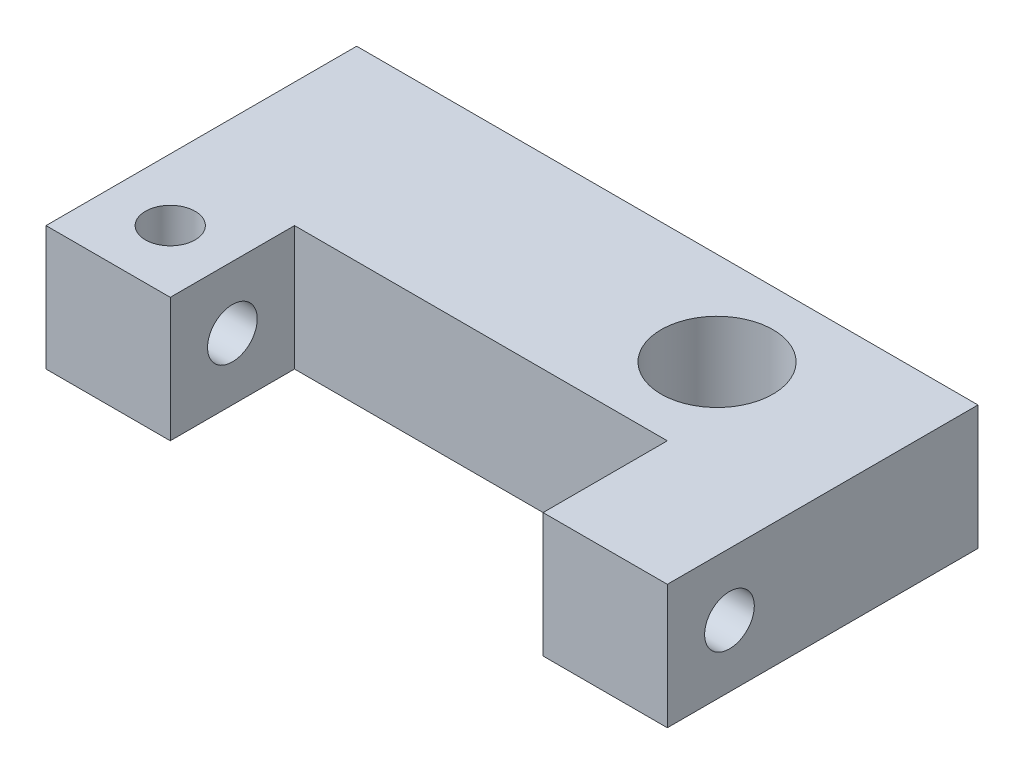
SolidWorks part; units mm, degrees
ref_plane "Plan de face" through (0, 0, 0) normal (0, 0, 1) x (1, 0, 0)
ref_plane "Plan de dessus" through (0, 0, 0) normal (0, 1, 0) x (1, 0, 0)
ref_plane "Plan de droite" through (0, 0, 0) normal (1, 0, 0) x (0, 0, -1)
sketch "Esquisse1" plane through (0, 0, 0) normal (0, 0, 1) x (1, 0, 0)
  line L5 (0, -3.3) -> (0, 3.3) construction
  line L6 (-10, 4) -> (10, 4)
  line L11 (-10, 4) -> (-10, 0)
  line L12 (-10, 0) -> (2.2, 0)
  line L13 (10, 4) -> (10, 0)
  line L14 (-10, 4) -> (10, 0) construction
  line L15 (-10, 0) -> (10, 4) construction
  line L16 (5.5, 0) -> (-5.5, 0) construction
  line L17 (7, 0) -> (10, 0)
  line L19 (2.2, 0) -> (2.2, -2)
  line L20 (2.2, -2) -> (7, -2)
  line L21 (7, 0) -> (7, -2)
  point P0 (0, 0)
  point P1 (0, 2)
  dimension "D1" = 4
  dimension "D2" = 2
  dimension "D3" = 4.8
  dimension "D4" = 20
  dimension "D5" = 3
extrude "Boss.-Extru.1" add sketch "Esquisse1" against normal blind 6
sketch "Esquisse2" plane through (0, 0, 0) normal (0, 0, 1) x (1, 0, 0)
  line L0 (-10, 4) -> (-10, 0) construction
  line L1 (0, -3.3) -> (0, 3.3) construction
  line L2 (-10, 4) -> (-6, 4)
  line L3 (-10, 4) -> (-10, 0)
  line L4 (-10, 0) -> (-6, 0)
  line L5 (-6, 4) -> (-6, 0)
  line L6 (10, 0) -> (6, 0)
  line L7 (6, 4) -> (6, 0)
  line L8 (10, 4) -> (6, 4)
  line L9 (10, 4) -> (10, 0)
  point P6 (-10, 2)
  dimension "D1" = 4
  dimension "D2" = 4
extrude "Boss.-Extru.2" add sketch "Esquisse2" along normal blind 4
hole_wizard "Trou pour taraudage pour trou taraudé M21" positions "Esquisse3" profile "Esquisse4" hole size "M2" standard "ISO" end condition through all
sketch "Esquisse3" plane through (10, 0, 0) normal (1, 0, 0) x (0, 0, -1)
  line L0 (-4, 2) -> (0, 2) construction
  line L1 (-4, 0) -> (-4, 4) construction
  line L2 (0, 3.3) -> (0, -3.3) construction
  line L5 (6, 4) -> (-4, 4) construction
  line L6 (-2, 4) -> (-2, 0) construction
  line L7 (5.5, 0) -> (-5.5, 0) construction
  point P0 (-2, 2)
  point P21 (-2, 2)
  point P22 (0, 0)
sketch "Esquisse4" plane through (10, 2, 2) normal (0, 1, 0) x (0, 0, -1)
  line L0 (0, 0) -> (0, 20)
  line L1 (0, 20) -> (0.8, 20)
  line L2 (0.8, 20) -> (0.8, 0)
  line L5 (0.8, 0) -> (0, 0)
  line L11 (0, -6.35) -> (0, 107.95) construction
  dimension "Diamètre du perçage jusqu'au prochain" = 1.6
  dimension "Profondeur du perçage jusqu'au prochain" = 20
hole_wizard "Trou pour taraudage pour trou taraudé M22" positions "Esquisse5" profile "Esquisse6" hole size "M2" standard "ISO"
sketch "Esquisse5" plane through (0, 4, 0) normal (0, 1, 0) x (1, 0, 0)
  line L0 (-6, -2) -> (-10, -2) construction
  line L1 (-6, -4) -> (-6, 0) construction
  line L2 (-10, 6) -> (-10, -4) construction
  point P0 (-8, -2)
  point P10 (0, 0)
  point P11 (-8, -2)
sketch "Esquisse6" plane through (-8, 4, 2) normal (1, 0, 0) x (0, 0, 1)
  line L0 (0, 0) -> (0, 1.2)
  line L1 (0, 1.2) -> (0.8, 1.2)
  line L2 (0.8, 1.2) -> (0.8, 0)
  line L5 (0.8, 0) -> (0, 0)
  line L11 (0, -6.35) -> (0, 107.95) construction
  dimension "Diamètre du perçage jusqu'au prochain" = 1.6
  dimension "Profondeur du perçage jusqu'au prochain" = 1.2
hole_wizard "Dégagement M31" positions "Esquisse7" profile "Esquisse8" hole size "M3" standard "ISO" end condition through all
sketch "Esquisse7" plane through (0, 4, 0) normal (0, 1, 0) x (1, 0, 0)
  line L0 (7, 6) -> (7, 0) construction
  line L1 (2.2, 6) -> (2.2, 0) construction
  line L2 (7, 6) -> (7, 0) construction
  line L3 (2.2, 6) -> (2.2, 0) construction
  line L4 (2.2, 3) -> (7, 3) construction
  point P0 (4.6, 3)
  point P11 (0, 0)
  point P12 (4.6, 3)
sketch "Esquisse8" plane through (4.6, 4, -3) normal (1, 0, 0) x (0, 0, 1)
  line L0 (0, 0) -> (0, 6)
  line L1 (0, 6) -> (1.8, 6)
  line L2 (1.8, 6) -> (1.8, 0)
  line L5 (1.8, 0) -> (0, 0)
  line L11 (0, -6.35) -> (0, 107.95) construction
  dimension "Diamètre du perçage jusqu'au prochain" = 3.6
  dimension "Profondeur du perçage jusqu'au prochain" = 6
